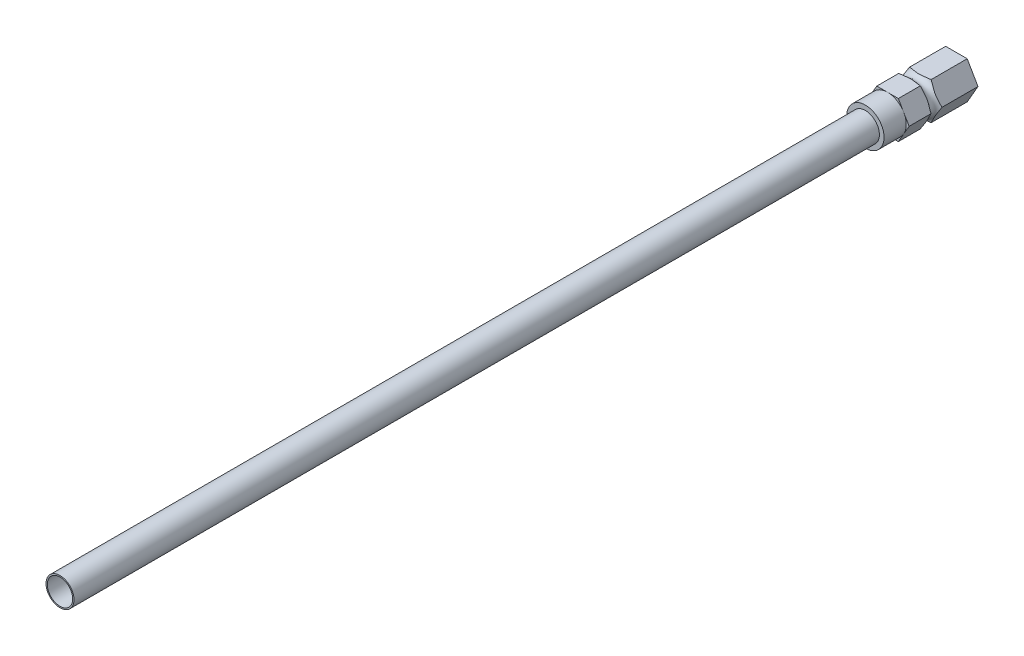
SolidWorks part; units mm, degrees
ref_plane "Front Plane" through (0, 0, 0) normal (0, 0, 1) x (1, 0, 0)
ref_plane "Top Plane" through (0, 0, 0) normal (0, 1, 0) x (1, 0, 0)
ref_plane "Right Plane" through (0, 0, 0) normal (1, 0, 0) x (0, 0, -1)
sketch "Sketch1" plane through (0, 0, 0) normal (0, 0, 1) x (1, 0, 0)
  circle A0 centre (0, 0) radius 9.525
  circle A1 centre (0, 0) radius 8.636
  dimension "D2" = 19.05
  dimension "D1" = 0.889
extrude "Boss-Extrude1" add sketch "Sketch1" along normal blind 609.6
ref_plane "Plane1" through (0, 0, -12.7) normal (0, 0, -1) x (-1, 0, 0)
sketch "Sketch2" plane through (0, 0, 0) normal (1, 0, 0) x (0, 0, -1)
  line L0 (0, 9.525) -> (0, 17.78)
  line L1 (0, 17.78) -> (-46.8312, 17.78)
  line L2 (-46.8312, 17.78) -> (-46.8312, 12.7)
  line L3 (-46.8312, 12.7) -> (-61.9125, 12.7)
  line L4 (-61.9125, 12.7) -> (-61.9125, 9.525)
  line L5 (-61.9125, 9.525) -> (0, 9.525)
  line L6 (0, 9.525) -> (-609.6, 9.525) construction
  line L7 (0, 0) -> (-118.3798, 0) construction
  line L9 (0, -9.525) -> (0, 9.525) construction
  circle A0 centre (-28.2394, 15.0812) radius 3.6901
  dimension "D1" = 17.78
  dimension "D2" = 15.0812
  dimension "D3" = 12.7
  dimension "D4" = 46.8312
  dimension "D5" = 61.9125
  dimension "D6" = 12.7
revolve "Revolve1" add sketch "Sketch2" angle 360 about L7
sketch "Sketch3" plane through (0, 0, 0) normal (0, 0, -1) x (-1, 0, 0)
  line L1 (14.6647, 0) -> (7.3323, 12.7)
  line L2 (7.3323, 12.7) -> (-7.3323, 12.7)
  line L3 (-7.3323, 12.7) -> (-14.6647, 0)
  line L4 (-14.6647, 0) -> (-7.3323, -12.7)
  line L5 (-7.3323, -12.7) -> (7.3323, -12.7)
  line L6 (7.3323, -12.7) -> (14.6647, 0)
  circle A0 centre (0, 0) radius 12.7 construction
  circle A1 centre (0, 0) radius 20.2468
  dimension "D1" = 25.4
extrude "Cut-Extrude1" cut sketch "Sketch3" against normal blind 101.6
